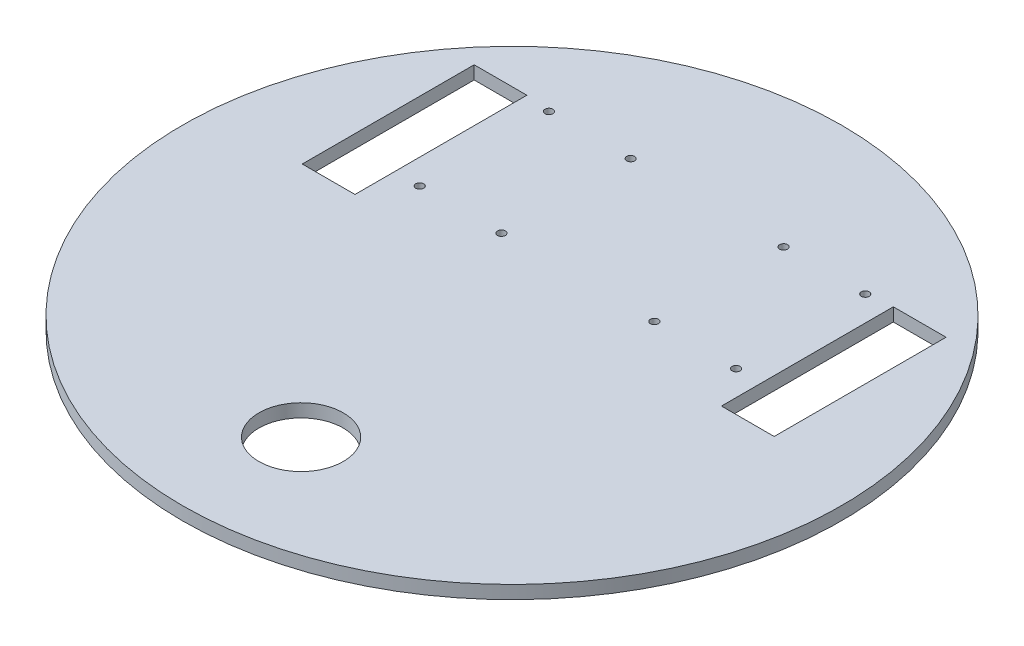
SolidWorks part; units mm, degrees
ref_plane "Front Plane" through (0, 0, 0) normal (0, 0, 1) x (1, 0, 0)
ref_plane "Top Plane" through (0, 0, 0) normal (0, 1, 0) x (1, 0, 0)
ref_plane "Right Plane" through (0, 0, 0) normal (1, 0, 0) x (0, 0, -1)
sketch "Sketch1" plane through (0, 0, 0) normal (0, 1, 0) x (1, 0, 0)
  line L0 (89.5, 2.9557) -> (69.5, 2.9557)
  line L5 (89.5, 68.1557) -> (89.5, 2.9557)
  line L6 (69.5, 2.9557) -> (69.5, 68.1557)
  line L7 (69.5, 68.1557) -> (89.5, 68.1557)
  line L8 (0, -140.0208) -> (0, 140.0208) construction
  line L9 (-69.5, 68.1557) -> (-89.5, 68.1557)
  line L10 (-69.5, 2.9557) -> (-69.5, 68.1557)
  line L11 (-89.5, 2.9557) -> (-69.5, 2.9557)
  line L12 (-89.5, 68.1557) -> (-89.5, 2.9557)
  circle A0 centre (0, -6.9886) radius 125
  circle A1 centre (0, -86.9886) radius 16
  circle A2 centre (60, 18.0114) radius 1.5
  circle A3 centre (60, 67.0114) radius 1.5
  circle A4 centre (29, 67.0114) radius 1.5
  circle A5 centre (29, 18.0114) radius 1.5
  circle A6 centre (-60, 18.0114) radius 1.5
  circle A7 centre (-29, 18.0114) radius 1.5
  circle A8 centre (-29, 67.0114) radius 1.5
  circle A9 centre (-60, 67.0114) radius 1.5
extrude "Boss-Extrude1" add sketch "Sketch1" along normal blind 5
